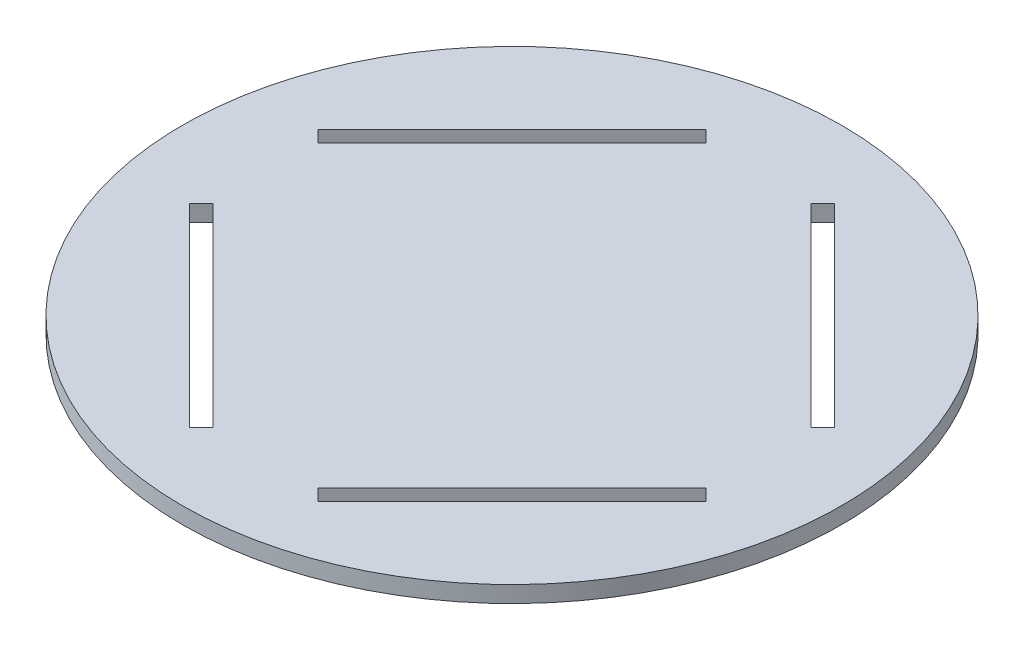
SolidWorks part; units mm, degrees
material "Acrylic (Medium-high impact)"
ref_plane "Plano frontal," through (0, 0, 0) normal (0, 0, 1) x (1, 0, 0)
ref_plane "Plano superior" through (0, 0, 0) normal (0, 1, 0) x (1, 0, 0)
ref_plane "Plano direito" through (0, 0, 0) normal (1, 0, 0) x (0, 0, -1)
sketch "Sketch1" plane through (0, 0, 0) normal (0, 1, 0) x (1, 0, 0)
  circle A0 centre (0, 0) radius 60
  dimension "D1" = 120
extrude "Boss-Extrude1" add sketch "Sketch1" along normal mid plane 3
sketch "Sketch4" plane through (0, 1.5, 0) normal (0, 1, 0) x (1, 0, 0)
  line L0 (9.5459, 44.9013) -> (44.9013, 9.5459)
  line L1 (9.5459, 44.9013) -> (11.6673, 47.0226)
  line L2 (44.9013, 9.5459) -> (47.0226, 11.6673)
  line L3 (11.6673, 47.0226) -> (47.0226, 11.6673)
  line L4 (9.5459, 44.9013) -> (47.0226, 11.6673) construction
  line L5 (44.9013, 9.5459) -> (11.6673, 47.0226) construction
  line L6 (0, 0) -> (28.2843, 28.2843) construction
  point P1 (28.2843, 28.2843)
  dimension "D1" = 3
  dimension "D2" = 50
  dimension "D3" = 40
  dimension "D4" = 45
extrude "Cut-Extrude3" cut sketch "Sketch4" against normal through all both and the other way through all
pattern_circular "CirPattern1" count 4 over 360 about axis through (0, 0, 0) along (0, 1, 0) of "Cut-Extrude3"
